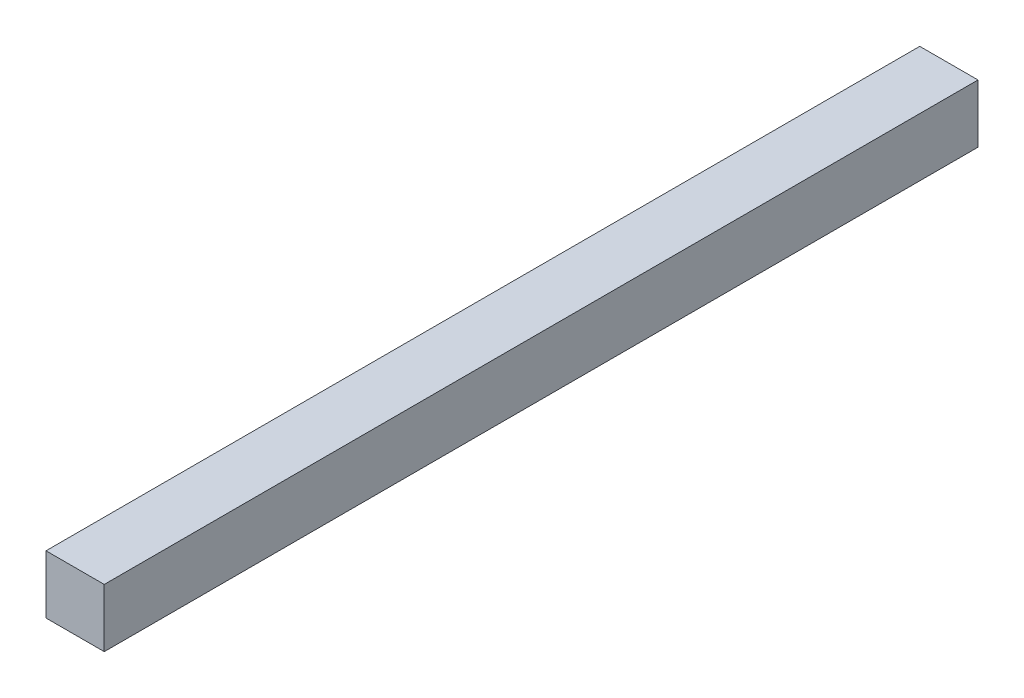
SolidWorks part; units mm, degrees
material "6061 Alloy"
ref_plane "Front Plane" through (0, 0, 0) normal (0, 0, 1) x (1, 0, 0)
ref_plane "Top Plane" through (0, 0, 0) normal (0, 1, 0) x (1, 0, 0)
ref_plane "Right Plane" through (0, 0, 0) normal (1, 0, 0) x (0, 0, -1)
sketch "Sketch1" plane through (0, 0, 0) normal (0, 0, 1) x (1, 0, 0)
  line L5 (-12.7, -12.7) -> (12.7, -12.7)
  line L6 (-12.7, -12.7) -> (-12.7, 12.7)
  line L7 (-12.7, 12.7) -> (12.7, 12.7)
  line L8 (12.7, -12.7) -> (12.7, 12.7)
  line L9 (-12.7, -12.7) -> (12.7, 12.7) construction
  line L10 (-12.7, 12.7) -> (12.7, -12.7) construction
  point P0 (0, 0)
  dimension "D1" = 25.4
  dimension "D2" = 25.4
extrude "Boss-Extrude1" add sketch "Sketch1" along normal blind 381
